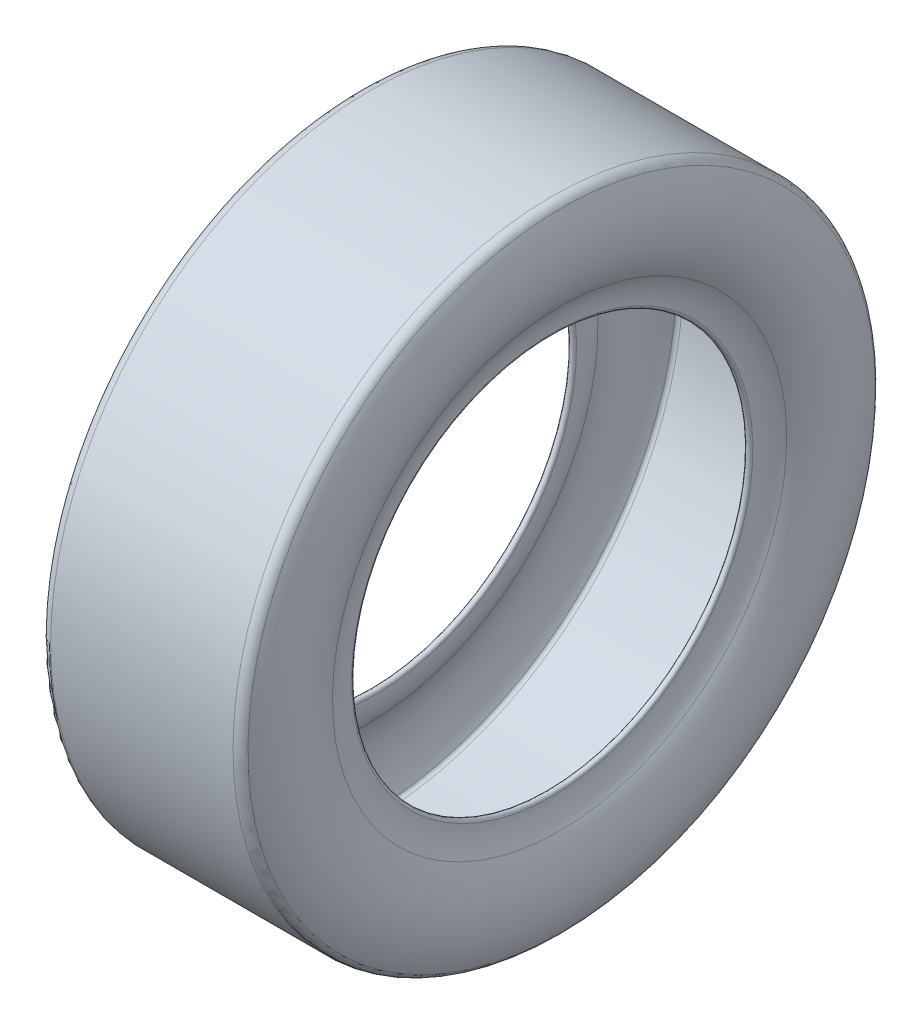
SolidWorks part; units mm, degrees
material "Rubber"
ref_plane "Front Plane" through (0, 0, 0) normal (0, 0, 1) x (1, 0, 0)
ref_plane "Top Plane" through (0, 0, 0) normal (0, 1, 0) x (1, 0, 0)
ref_plane "Right Plane" through (0, 0, 0) normal (1, 0, 0) x (0, 0, -1)
sketch "Sketch3" plane through (0, 0, 0) normal (0, 0, 1) x (1, 0, 0)
  line L0 (-76.2, 266.7) -> (76.2, 266.7)
  line L1 (0, -55) -> (0, 55) construction
  line L2 (-76.2, 261.62) -> (76.2, 261.62)
  line L3 (-23.1787, 0) -> (23.1787, 0) construction
  line L4 (55, 0) -> (-55, 0) construction
  line L5 (0, 266.7) -> (0, 0) construction
  arc A0 (-76.2, 266.7) -> (-84.0362, 262.0045) centre (-76.2, 257.8135) ccw
  arc A1 (-71.12, 167.64) -> (-77.9408, 192.3265) centre (-119.2044, 167.64) ccw
  arc A2 (-77.9408, 192.3265) -> (-79.5566, 259.6087) centre (-19.3241, 227.3947) cw
  arc A3 (-84.0362, 262.0045) -> (-82.3002, 189.7184) centre (-19.3241, 227.3947) ccw
  arc A4 (-82.3002, 189.7184) -> (-76.2, 167.64) centre (-119.2044, 167.64) cw
  arc A5 (-76.2, 167.64) -> (-71.12, 167.64) centre (-73.66, 167.64) ccw
  arc A6 (-79.5566, 259.6087) -> (-76.2, 261.62) centre (-76.2, 257.8135) cw
  arc A7 (76.2, 167.64) -> (71.12, 167.64) centre (73.66, 167.64) cw
  arc A8 (71.12, 167.64) -> (77.9408, 192.3265) centre (119.2044, 167.64) cw
  arc A9 (82.3002, 189.7184) -> (76.2, 167.64) centre (119.2044, 167.64) ccw
  arc A10 (77.9408, 192.3265) -> (79.5566, 259.6087) centre (19.3241, 227.3947) ccw
  arc A11 (84.0362, 262.0045) -> (82.3002, 189.7184) centre (19.3241, 227.3947) cw
  arc A12 (79.5566, 259.6087) -> (76.2, 261.62) centre (76.2, 257.8135) ccw
  arc A13 (76.2, 266.7) -> (84.0362, 262.0045) centre (76.2, 257.8135) cw
  point P2 (0, 266.7)
  dimension "D3" = 92.71
  dimension "D4" = 2.54
  dimension "D5" = 165.1
  dimension "D1" = 152.4
  dimension "D2" = 266.7
  dimension "D6" = 76.2
revolve "Tire" add sketch "Sketch3" angle 360 about L3
sketch "Tire Patch Locater" plane through (0, 0, 0) normal (1, 0, 0) x (0, 0, -1)
  circle A0 centre (0, 0) radius 266.7 construction
